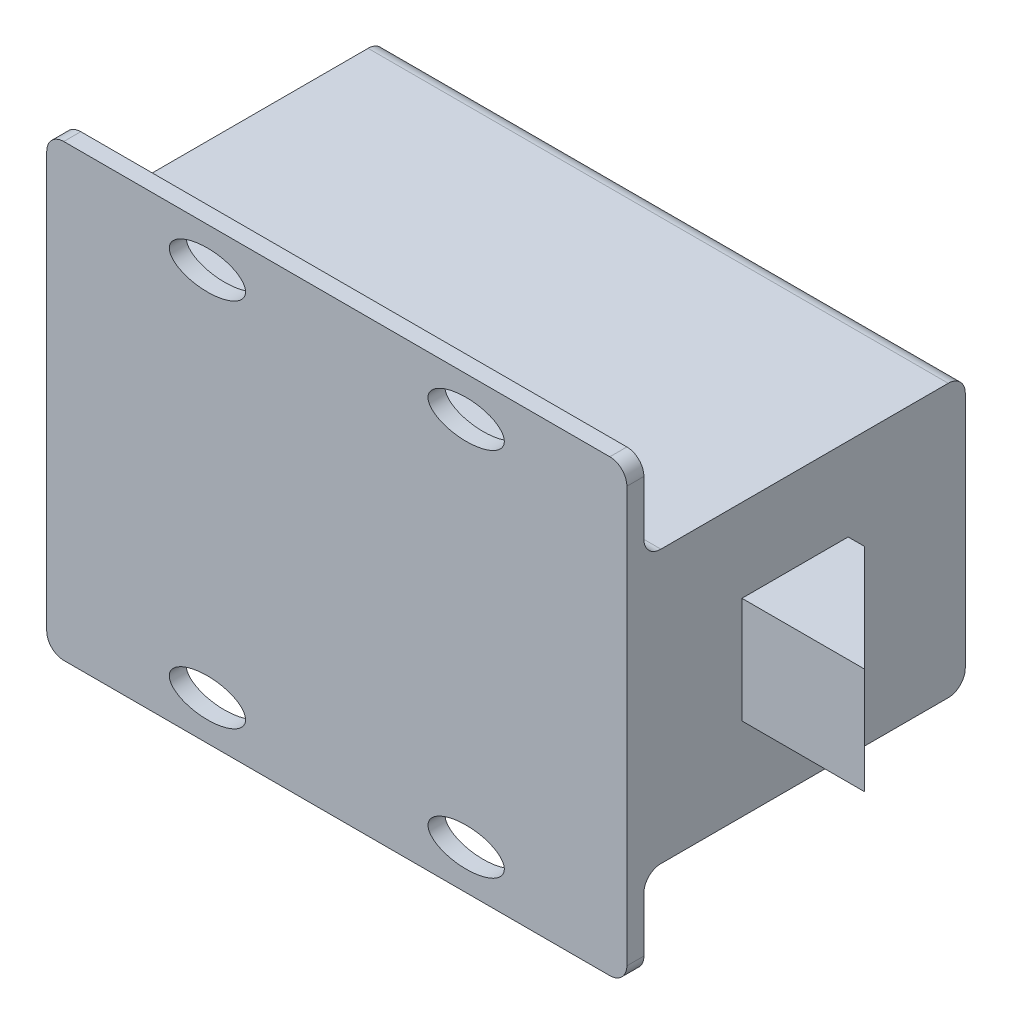
SolidWorks part; units mm, degrees
ref_plane "Front Plane" through (0, 0, 0) normal (0, 0, 1) x (1, 0, 0)
ref_plane "Top Plane" through (0, 0, 0) normal (0, 1, 0) x (1, 0, 0)
ref_plane "Right Plane" through (0, 0, 0) normal (1, 0, 0) x (0, 0, -1)
sketch "Sketch1" plane through (0, 0, 0) normal (0, 0, 1) x (1, 0, 0)
  line L1 (-27.051, -20.955) -> (27.051, -20.955)
  line L2 (-27.051, -20.955) -> (-27.051, 20.955)
  line L3 (-27.051, 20.955) -> (27.051, 20.955)
  line L4 (27.051, -20.955) -> (27.051, 20.955)
  line L5 (-27.051, -20.955) -> (27.051, 20.955) construction
  line L6 (-27.051, 20.955) -> (27.051, -20.955) construction
  point P0 (0, 0)
  dimension "D1" = 54.102
  dimension "D2" = 41.91
extrude "Boss-Extrude1" add sketch "Sketch1" along normal blind 1.5875
fillet "Fillet1" radius 1.5875 4 edges at (27.051, -20.955, 0.7937) (-27.051, -20.955, 0.7937) (-27.051, 20.955, 0.7937) (27.051, 20.955, 0.7937)
sketch "Sketch2" plane through (0, 0, 0) normal (0, 0, -1) x (-1, 0, 0)
  line L1 (-27.051, -12.7) -> (27.051, -12.7)
  line L2 (-27.051, -12.7) -> (-27.051, 12.7)
  line L3 (-27.051, 12.7) -> (27.051, 12.7)
  line L4 (27.051, -12.7) -> (27.051, 12.7)
  line L5 (-27.051, -12.7) -> (27.051, 12.7) construction
  line L6 (-27.051, 12.7) -> (27.051, -12.7) construction
  point P0 (0, 0)
  dimension "D1" = 54.102
  dimension "D2" = 25.4
extrude "Boss-Extrude2" add sketch "Sketch2" along normal blind 29.972
fillet "Fillet2" radius 1.5875 2 edges at (0, -12.7, 0) (0, 12.7, 0)
fillet "Fillet3" radius 1.5875 2 edges at (0, -12.7, -29.972) (0, 12.7, -29.972)
sketch "Sketch3" plane through (0, 0, 0) normal (0, 0, -1) x (-1, 0, 0)
  line L0 (-27.051, -19.3675) -> (-27.051, -14.2875) construction
  line L1 (0, 17.3577) -> (0, -17.3577) construction
  line L2 (17.3577, 0) -> (-17.3577, 0) construction
  ellipse E0 centre (-12.065, -17.2743) end of major axis (-15.621, -17.2743) minor radius 1.778
  ellipse E1 centre (12.065, -17.2743) end of major axis (15.621, -17.2743) minor radius 1.778
  ellipse E2 centre (12.065, 17.2743) end of major axis (15.621, 17.2743) minor radius 1.778
  ellipse E3 centre (-12.065, 17.2743) end of major axis (-15.621, 17.2743) minor radius 1.778
  dimension "D1" = 3.556
  dimension "D2" = 7.112
  dimension "D3" = 14.986
extrude "Cut-Extrude1" cut sketch "Sketch3" against normal through all
sketch "Sketch4" plane through (27.051, 0, 0) normal (1, 0, 0) x (0, 0, -1)
  line L0 (28.3845, 12.7) -> (1.5875, 12.7) construction
  line L1 (19.05, -4.953) -> (9.144, -4.953)
  line L2 (19.05, -4.953) -> (19.05, 4.953)
  line L3 (19.05, 4.953) -> (9.144, 4.953)
  line L4 (9.144, -4.953) -> (9.144, 4.953)
  line L5 (19.05, -4.953) -> (9.144, 4.953) construction
  line L6 (19.05, 4.953) -> (9.144, -4.953) construction
  line L8 (29.972, 11.1125) -> (29.972, -11.1125) construction
  point P0 (14.097, 0)
  dimension "D1" = 9.906
  dimension "D2" = 9.906
  dimension "D3" = 12.7
  dimension "D4" = 15.875
extrude "Boss-Extrude3" add sketch "Sketch4" along normal blind 11.43 contours L2 L1 L4 L3
sketch "Sketch6" plane through (0, 4.953, 0) normal (0, 1, 0) x (1, 0, 0)
  line L0 (38.481, 9.144) -> (28.575, 19.05)
  line L2 (38.481, 19.05) -> (27.051, 19.05) construction
  line L3 (38.481, 19.05) -> (38.481, 9.144) construction
  line L4 (38.481, 9.144) -> (38.481, 19.05)
  line L5 (38.481, 19.05) -> (28.575, 19.05)
  dimension "D1" = 45
extrude "Cut-Extrude2" cut sketch "Sketch6" against normal through all
